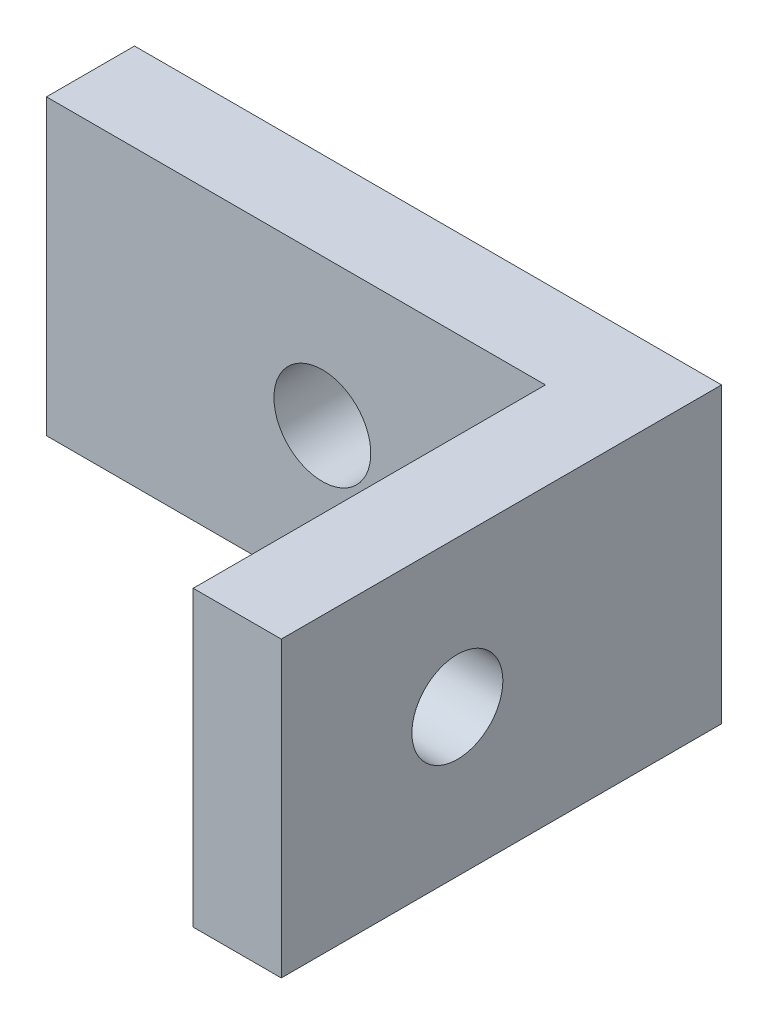
SolidWorks part; units mm, degrees
ref_plane "Alzado" through (0, 0, 0) normal (0, 0, 1) x (1, 0, 0)
ref_plane "Planta" through (0, 0, 0) normal (0, 1, 0) x (1, 0, 0)
ref_plane "Vista lateral" through (0, 0, 0) normal (1, 0, 0) x (0, 0, -1)
sketch "Sketch1" plane through (0, 0, 0) normal (0, 1, 0) x (1, 0, 0)
  line L0 (0, 0) -> (17, 0)
  line L1 (17, 0) -> (17, -12)
  line L2 (17, -12) -> (20, -12)
  line L3 (20, -12) -> (20, 3)
  line L4 (20, 3) -> (0, 3)
  line L5 (0, 3) -> (0, 0)
  dimension "D1" = 20
  dimension "D2" = 15
  dimension "D3" = 3
extrude "Boss-Extrude1" add sketch "Sketch1" along normal blind 10
sketch "Sketch2" plane through (20, 0, 0) normal (1, 0, 0) x (0, 0, -1)
  line L0 (3, 10) -> (3, 0) construction
  line L1 (-12, 10) -> (-12, 0) construction
  circle A0 centre (-6, 5) radius 1.55
  point P2 (0, 0)
  point P5 (-6, 4.6803)
  point P8 (-12, 5)
extrude "Cut-Extrude1" cut sketch "Sketch2" against normal up to next
sketch "Sketch3" plane through (0, 0, -3) normal (0, 0, -1) x (-1, 0, 0)
  line L0 (-20, 10) -> (-20, 0) construction
  line L1 (0, 10) -> (0, 0) construction
  circle A0 centre (-9.4, 5) radius 1.65
  point P4 (-20, 5)
extrude "Cut-Extrude2" cut sketch "Sketch3" against normal up to next
equation "\"Squares_Tolerance\"= 0.2"
equation "\"Circle_Tolerance\"= 0.1"
equation "\"D1@Sketch2\"=\"Circle_Tolerance\"+3"
equation "\"D2@Sketch3\"=\"Circle_Tolerance\"+9.3"
